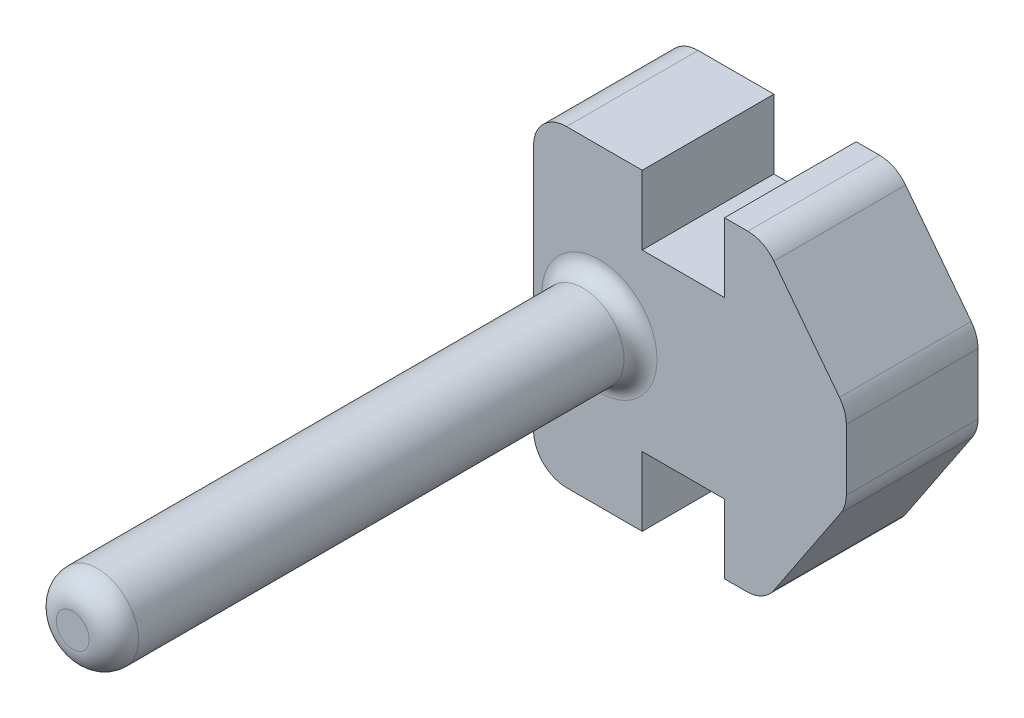
SolidWorks part; units mm, degrees
ref_plane "Front Plane" through (0, 0, 0) normal (0, 0, 1) x (1, 0, 0)
ref_plane "Top Plane" through (0, 0, 0) normal (0, 1, 0) x (1, 0, 0)
ref_plane "Right Plane" through (0, 0, 0) normal (1, 0, 0) x (0, 0, -1)
sketch "Sketch1" plane through (0, 0, 0) normal (0, 0, 1) x (1, 0, 0)
  line L1 (3.5, -4.75) -> (-3.5, -4.75)
  line L2 (3.5, -4.75) -> (3.5, 4.75)
  line L3 (3.5, 4.75) -> (-3.5, 4.75)
  line L4 (-3.5, -4.75) -> (-3.5, 4.75)
  line L5 (3.5, -4.75) -> (-3.5, 4.75) construction
  line L6 (3.5, 4.75) -> (-3.5, -4.75) construction
  line L7 (-0.2, 4.75) -> (2.3, 4.75)
  line L8 (-0.2, 4.75) -> (-0.2, 2.65)
  line L9 (-0.2, 2.65) -> (2.3, 2.65)
  line L10 (2.3, 4.75) -> (2.3, 2.65)
  line L11 (-0.2, -4.75) -> (2.3, -4.75)
  line L12 (-0.2, -4.75) -> (-0.2, -2.65)
  line L13 (-0.2, -2.65) -> (2.3, -2.65)
  line L14 (2.3, -4.75) -> (2.3, -2.65)
  point P0 (0, 0)
  dimension "D1" = 7
  dimension "D2" = 9.5
  dimension "D3" = 2.1
  dimension "D4" = 2.1
  dimension "D5" = 2.5
  dimension "D6" = 2.5
  dimension "D7" = 3.3
  dimension "D8" = 3.3
extrude "Boss-Extrude1" add sketch "Sketch1" along normal blind 4 contours L14 L1 L2 L3 L10 L9 L8 L4 L12 L13
sketch "Sketch2" plane through (0, 0, 0) normal (0, 0, -1) x (-1, 0, 0)
  line L0 (-3.5, 4.75) -> (-6, 1.5)
  line L1 (-6, 1.5) -> (-6, -1)
  line L2 (-6, -1) -> (-3.5, -4.75)
  line L12 (-2.3, -4.75) -> (-2.3, -2.65)
  line L13 (-2.3, -2.65) -> (0.2, -2.65)
  line L14 (0.2, -2.65) -> (0.2, -4.75)
  line L15 (0.2, -4.75) -> (3.5, -4.75)
  line L16 (3.5, -4.75) -> (3.5, 4.75)
  line L17 (3.5, 4.75) -> (0.2, 4.75)
  line L18 (0.2, 4.75) -> (0.2, 2.65)
  line L19 (0.2, 2.65) -> (-2.3, 2.65)
  line L20 (-2.3, 2.65) -> (-2.3, 4.75)
  line L21 (-2.3, 4.75) -> (-3.5, 4.75)
  line L22 (-3.5, 4.75) -> (-3.5, -4.75)
  line L23 (-3.5, -4.75) -> (-2.3, -4.75)
  line L24 (-2.3, -4.75) -> (-2.3, -2.65)
  line L25 (-2.3, -2.65) -> (0.2, -2.65)
  line L26 (0.2, -2.65) -> (0.2, -4.75)
  line L27 (0.2, -4.75) -> (3.5, -4.75)
  line L28 (3.5, -4.75) -> (3.5, 4.75)
  line L29 (3.5, 4.75) -> (0.2, 4.75)
  line L30 (0.2, 4.75) -> (0.2, 2.65)
  line L31 (0.2, 2.65) -> (-2.3, 2.65)
  line L32 (-2.3, 2.65) -> (-2.3, 4.75)
  line L33 (-2.3, 4.75) -> (-3.5, 4.75)
  line L34 (-3.5, 4.75) -> (-3.5, -4.75)
  line L35 (-3.5, -4.75) -> (-2.3, -4.75)
  line M23 (-3.5, 4.75) -> (-3.5, -4.75)
  dimension "D2" = 2.5
  dimension "D3" = 2.5
  dimension "D4" = 3.25
  dimension "D1" = 0
extrude "Boss-Extrude2" add sketch "Sketch2" against normal blind 4 contours L1 L2 L0 M23
sketch "Sketch3" plane through (0, 0, 4) normal (0, 0, 1) x (1, 0, 0)
  line L12 (3.5, -4.75) -> (6, -1)
  line L14 (2.3, -2.65) -> (2.3, -4.75)
  line L15 (2.3, -4.75) -> (3.5, -4.75)
  line L18 (3.5, -4.75) -> (6, -1)
  line L19 (3.5, 4.75) -> (2.3, 4.75)
  line L20 (2.3, 4.75) -> (2.3, 2.65)
  line L21 (2.3, 2.65) -> (-0.2, 2.65)
  line L22 (-0.2, 2.65) -> (-0.2, 4.75)
  line L23 (-0.2, 4.75) -> (-3.5, 4.75)
  line L24 (-3.5, 4.75) -> (-3.5, -4.75)
  line L25 (-3.5, -4.75) -> (-0.2, -4.75)
  line L26 (-0.2, -4.75) -> (-0.2, -2.65)
  line L27 (-0.2, -2.65) -> (2.3, -2.65)
  line L28 (2.3, -2.65) -> (2.3, -4.75)
  line L29 (2.3, -4.75) -> (3.5, -4.75)
  line L33 (3.5, 4.75) -> (2.3, 4.75)
  line L34 (2.3, 4.75) -> (2.3, 2.65)
  line L35 (2.3, 2.65) -> (-0.2, 2.65)
  line L36 (-0.2, 2.65) -> (-0.2, 4.75)
  line L37 (-0.2, 4.75) -> (-3.5, 4.75)
  line L38 (-3.5, 4.75) -> (-3.5, -4.75)
  line L39 (-3.5, -4.75) -> (-0.2, -4.75)
  line L40 (-0.2, -4.75) -> (-0.2, -2.65)
  line L41 (-0.2, -2.65) -> (2.3, -2.65)
  line L42 (6, -1) -> (6, 1.5)
  line L43 (6, -1) -> (6, 1.5)
  line L44 (6, 1.5) -> (3.5, 4.75)
  line L45 (6, 1.5) -> (3.5, 4.75)
  circle A0 centre (-1.5, 0) radius 1.25
  dimension "D2" = 2.5
  dimension "D3" = 2
  dimension "D4" = 4.75
  dimension "D1" = 0
extrude "Boss-Extrude3" add sketch "Sketch3" along normal blind 16 contours A0
fillet "Fillet1" radius 1 6 edges at (3.5, -4.75, 2) (6, -1, 2) (6, 1.5, 2) (3.5, 4.75, 2) (-3.5, -4.75, 2) (-3.5, 4.75, 2)
fillet "Fillet2" radius 0.5 1 edges at (-0.25, 0, 4)
fillet "Fillet3" radius 0.75 1 edges at (-0.25, 0, 20)
